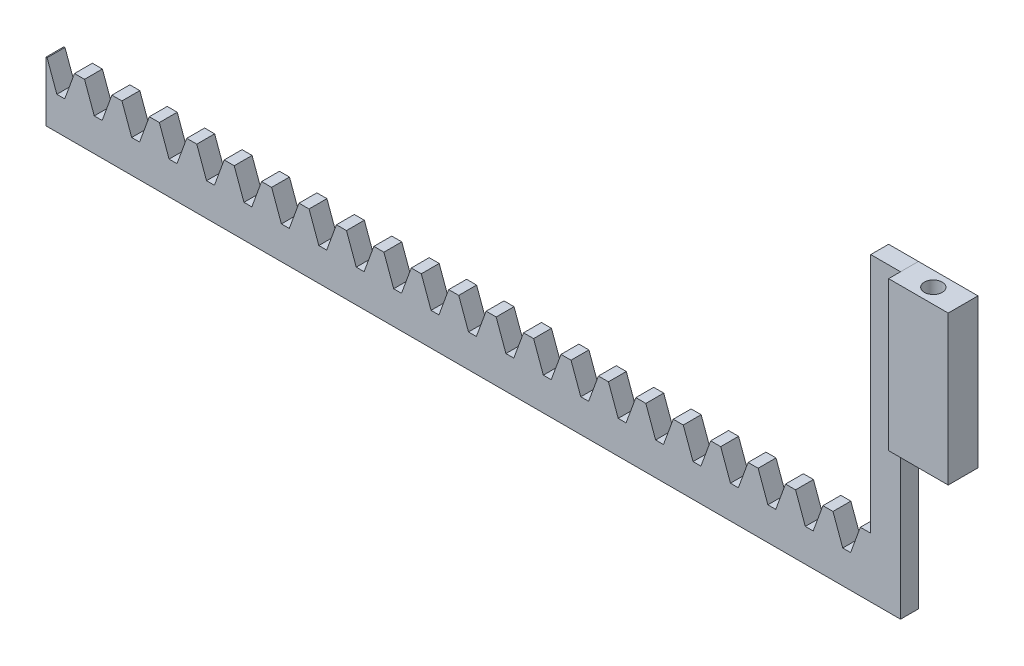
SolidWorks part; units mm, degrees
ref_plane "정면" through (0, 0, 0) normal (0, 0, 1) x (1, 0, 0)
ref_plane "윗면" through (0, 0, 0) normal (0, 1, 0) x (1, 0, 0)
ref_plane "우측면" through (0, 0, 0) normal (1, 0, 0) x (0, 0, -1)
sketch "스케치1" plane through (0, 0, 0) normal (0, 0, 1) x (1, 0, 0)
  line L1 (-76.7, 10) -> (76.7, 10)
  line L2 (-76.7, 10) -> (-76.7, 0)
  line L3 (-76.7, 0) -> (76.7, 0)
  line L4 (76.7, 10) -> (76.7, 0)
  dimension "D1" = 153.4
  dimension "D2" = 10
extrude "보스-돌출1" add sketch "스케치1" against normal blind 3
sketch "스케치2" plane through (0, 0, 0) normal (0, 0, 1) x (1, 0, 0)
  line L0 (-67.94, 10) -> (-67.94, 5.5) construction
  line L1 (-68.6001, 5.5) -> (-67.2799, 5.5)
  line L2 (-67.2799, 5.5) -> (-65.6421, 10)
  line L3 (-65.6421, 10) -> (-70.2379, 10)
  line L4 (-68.6001, 5.5) -> (-70.2379, 10)
  line L5 (-69.51, 8) -> (-66.37, 8)
  line L6 (-76.7, 10) -> (-76.7, 0) construction
  line L7 (76.7, 10) -> (-76.7, 10) construction
  line M10 (76.7, 10) -> (-76.7, 10)
  dimension "D1" = 2
  dimension "D2" = 4.5
  dimension "D3" = 40
  dimension "D4" = 8.76
  dimension "D5" = 3.14
extrude "컷-돌출1" cut sketch "스케치2" against normal through all contours L0 L3 L4 L5 | L0 L5 L2 M10 | L5 L0 L1 L2 | L0 L5 L4 L1
pattern_linear "선형 패턴1" count 21 spacing 6.28 along (1, 0, 0) count 2 spacing 6.28 along (-1, 0, 0) of "컷-돌출1"
sketch "스케치3" plane through (0, 0, 0) normal (0, -1, 0) x (1, 0, 0)
  line L1 (76.7, -3) -> (66.7, -3)
  line L2 (76.7, -3) -> (76.7, 0)
  line L3 (76.7, 0) -> (66.7, 0)
  line L4 (66.7, -3) -> (66.7, 0)
  dimension "D1" = 10
  dimension "D2" = 3
extrude "컷-돌출2" cut sketch "스케치3" against normal through all
ref_plane "평면1" through (0, 0, 0) normal (0, -1, 0) x (-1, 0, 0)
ref_plane "평면2" through (0, 10, 0) normal (0, 1, 0) x (1, 0, 0)
sketch "스케치4" plane through (0, 10, 0) normal (0, 1, 0) x (1, 0, 0)
  line L0 (66.7, 0) -> (59.9579, 0) construction
  line L1 (66.7, 3) -> (61.7, 3)
  line L2 (66.7, 3) -> (66.7, 0)
  line L3 (66.7, 0) -> (61.7, 0)
  line L4 (61.7, 3) -> (61.7, 0)
  dimension "D1" = 5
extrude "보스-돌출2" add sketch "스케치4" along normal blind 40.5
ref_plane "평면3" through (0, 0, -3) normal (0, 0, -1) x (-1, 0, 0)
sketch "스케치5" plane through (0, 0, -3) normal (0, 0, -1) x (-1, 0, 0)
  line L1 (-66.7, 25.5) -> (-76.7, 25.5)
  line L2 (-66.7, 25.5) -> (-66.7, 50.5)
  line L3 (-66.7, 50.5) -> (-76.7, 50.5)
  line L4 (-76.7, 25.5) -> (-76.7, 50.5)
  dimension "D1" = 25
  dimension "D2" = 10
extrude "보스-돌출3" add sketch "스케치5" against normal blind 5 separate body
ref_plane "평면4" through (0, 50.5, 0) normal (0, 1, 0) x (1, 0, 0)
sketch "스케치6" plane through (0, 50.5, 0) normal (0, 1, 0) x (1, 0, 0)
  line L0 (76.7, -2) -> (76.7, 3) construction
  line L1 (66.7, -2) -> (76.7, -2) construction
  circle A0 centre (71.7, 0.5) radius 1.5
  dimension "D1" = 5
  dimension "D2" = 2.5
extrude "컷-돌출3" cut sketch "스케치6" against normal blind 5
ref_plane "평면5" through (0, 25.5, 0) normal (0, -1, 0) x (-1, 0, 0)
sketch "스케치7" plane through (0, 25.5, 0) normal (0, -1, 0) x (-1, 0, 0)
  line L0 (-76.7, -2) -> (-76.7, 3) construction
  line L1 (-76.7, -2) -> (-66.7, -2) construction
  circle A0 centre (-71.7, 0.5) radius 1.5
  dimension "D1" = 3
  dimension "D2" = 5
  dimension "D3" = 2.5
extrude "컷-돌출4" cut sketch "스케치7" against normal blind 5
